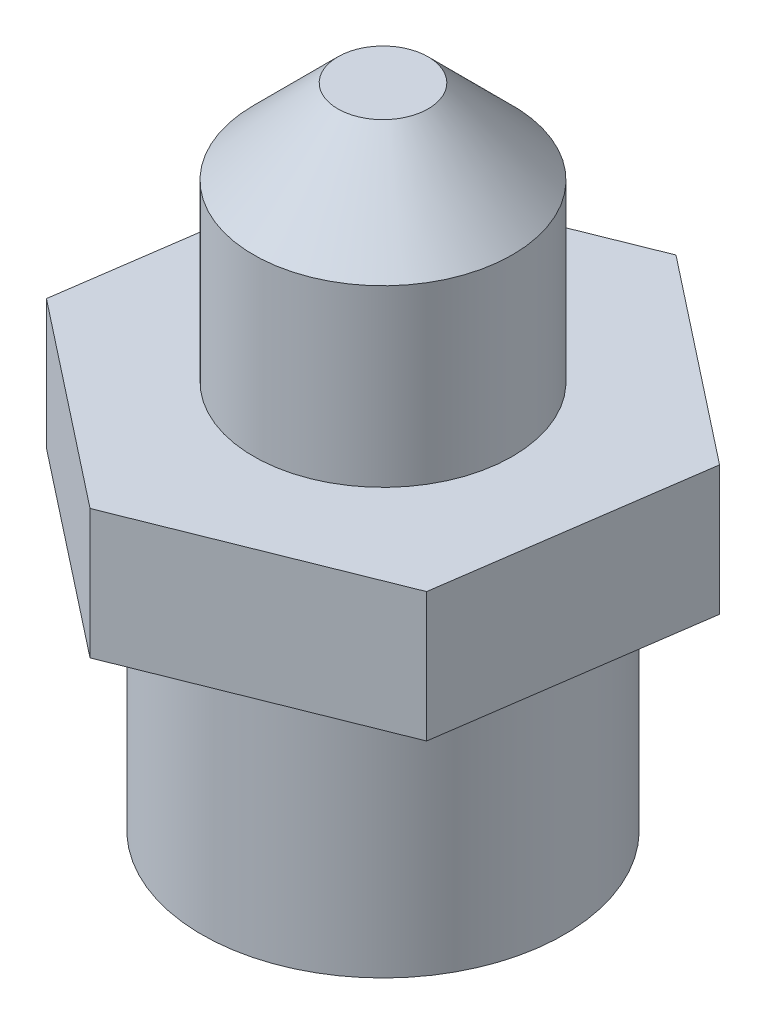
SolidWorks part; units mm, degrees
ref_plane "Спереди" through (0, 0, 0) normal (0, 0, 1) x (1, 0, 0)
ref_plane "Сверху" through (0, 0, 0) normal (0, 1, 0) x (1, 0, 0)
ref_plane "Справа" through (0, 0, 0) normal (1, 0, 0) x (0, 0, -1)
sketch "Эскиз1" plane through (0, 0, 0) normal (0, 0, 1) x (1, 0, 0)
  line L0 (0, 0) -> (7, 0)
  line L1 (7, 0) -> (7, 10)
  line L2 (7, 10) -> (10, 10)
  line L3 (10, 10) -> (10, 15)
  line L4 (10, 15) -> (5, 15)
  line L5 (5, 15) -> (5, 21.7442)
  line L6 (5, 21.7442) -> (1.7442, 25)
  line L7 (1.7442, 25) -> (0, 25)
  line L8 (0, 25) -> (0, 0) construction
  line L9 (0, 0) -> (0, 25)
  dimension "D1" = 7
  dimension "D2" = 10
  dimension "D3" = 5
  dimension "D4" = 25
  dimension "D5" = 5
  dimension "D6" = 10
revolve "Повернуть1" add sketch "Эскиз1" angle 360 about L8
sketch "Эскиз2" plane through (0, 15, 0) normal (0, 1, 0) x (1, 0, 0)
  line L1 (7.8627, -6.1788) -> (9.2824, 3.7199)
  line L2 (9.2824, 3.7199) -> (1.4197, 9.8987)
  line L3 (1.4197, 9.8987) -> (-7.8627, 6.1788)
  line L4 (-7.8627, 6.1788) -> (-9.2824, -3.7199)
  line L5 (-9.2824, -3.7199) -> (-1.4197, -9.8987)
  line L6 (-1.4197, -9.8987) -> (7.8627, -6.1788)
  circle A0 centre (0, 0) radius 8.6603 construction
extrude "Вырез-Вытянуть1" cut sketch "Эскиз2" against normal through all flip side to cut
